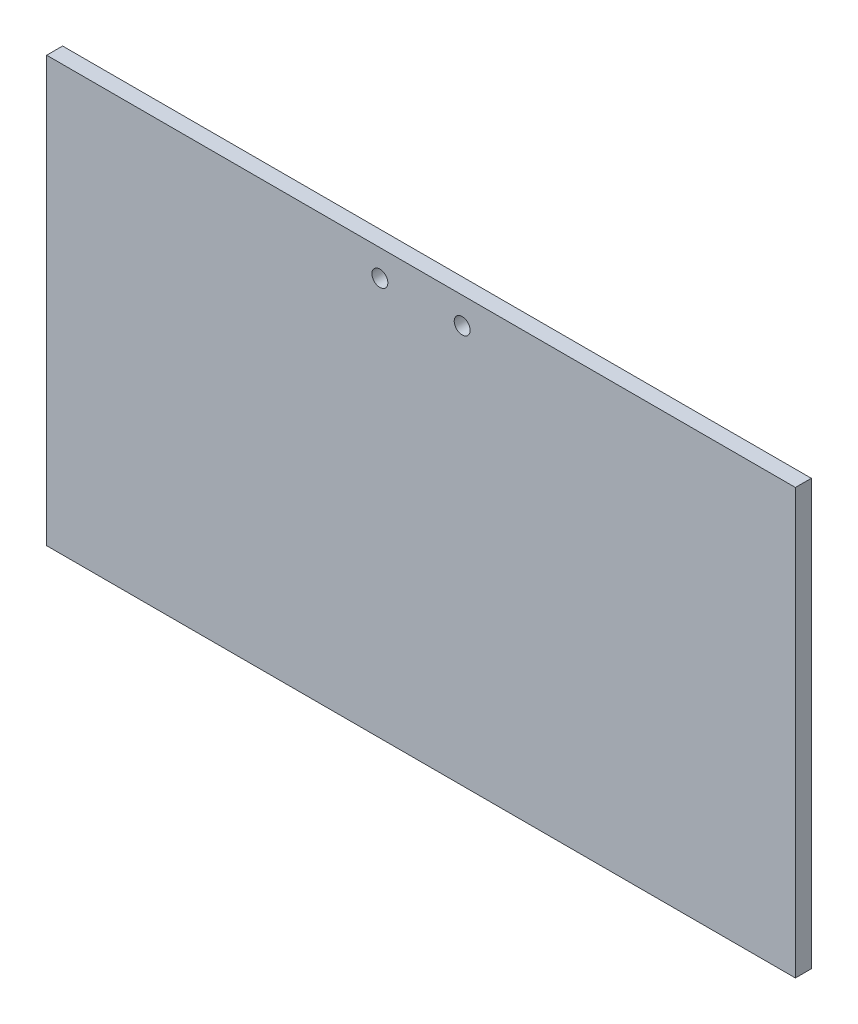
SolidWorks part; units mm, degrees
material "ｱｸﾘﾙ (中-上級の耐衝撃性)"
ref_plane "正面" through (0, 0, 0) normal (0, 0, 1) x (1, 0, 0)
ref_plane "平面" through (0, 0, 0) normal (0, 1, 0) x (1, 0, 0)
ref_plane "右側面" through (0, 0, 0) normal (1, 0, 0) x (0, 0, -1)
sketch "ｽｹｯﾁ1" plane through (0, 0, 0) normal (0, 0, 1) x (1, 0, 0)
  line L1 (-39.9942, 37.4101) -> (101.0058, 37.4101)
  line L2 (-39.9942, 37.4101) -> (-39.9942, -42.5899)
  line L3 (-39.9942, -42.5899) -> (101.0058, -42.5899)
  line L4 (101.0058, 37.4101) -> (101.0058, -42.5899)
  dimension "D1" = 80
  dimension "D2" = 141
extrude "ﾎﾞｽ - 押し出し1" add sketch "ｽｹｯﾁ1" against normal blind 3
sketch "ｽｹｯﾁ2" plane through (0, 0, 0) normal (0, 0, 1) x (1, 0, 0)
  line L0 (30.5058, 37.4101) -> (30.5058, -42.5899) construction
  line L1 (101.0058, 37.4101) -> (-39.9942, 37.4101) construction
  line L2 (-39.9942, -42.5899) -> (101.0058, -42.5899) construction
  line L3 (-39.9942, 32.4101) -> (101.0058, 32.4101) construction
  line L4 (-39.9942, 37.4101) -> (-39.9942, -42.5899) construction
  line L5 (101.0058, -42.5899) -> (101.0058, 37.4101) construction
  circle A0 centre (22.7558, 32.4101) radius 1.5
  circle A1 centre (38.2558, 32.4101) radius 1.5
  dimension "D2" = 3
  dimension "D3" = 3
  dimension "D4" = 7.75
  dimension "D5" = 7.75
  dimension "D1" = 5
extrude "ｶｯﾄ - 押し出し1" cut sketch "ｽｹｯﾁ2" against normal through all
sketch "ｽｹｯﾁ3" plane through (0, 0, 0) normal (0, 0, 1) x (1, 0, 0)
  line L0 (-4.4942, 37.4101) -> (-4.4942, -42.5899)
  line L1 (101.0058, 37.4101) -> (-39.9942, 37.4101) construction
  line L2 (-39.9942, -42.5899) -> (101.0058, -42.5899) construction
  line L3 (65.5058, 37.4101) -> (65.5058, -42.5899)
  line L4 (-39.9942, 37.4101) -> (-39.9942, -42.5899) construction
  line L5 (101.0058, -42.5899) -> (101.0058, 37.4101) construction
  dimension "D1" = 35.5
  dimension "D2" = 35.5
sketch "ｽｹｯﾁ4" plane through (0, 37.4101, 0) normal (0, 1, 0) x (1, 0, 0)
  line L0 (-4.4942, 0) -> (-4.4942, 3)
  line L1 (101.0058, 0) -> (-39.9942, 0) construction
  line L2 (101.0058, 3) -> (-39.9942, 3) construction
  line L4 (65.5058, 0) -> (65.5058, 3)
  line L5 (101.0058, 3) -> (101.0058, 0) construction
  dimension "D1" = 35.5
